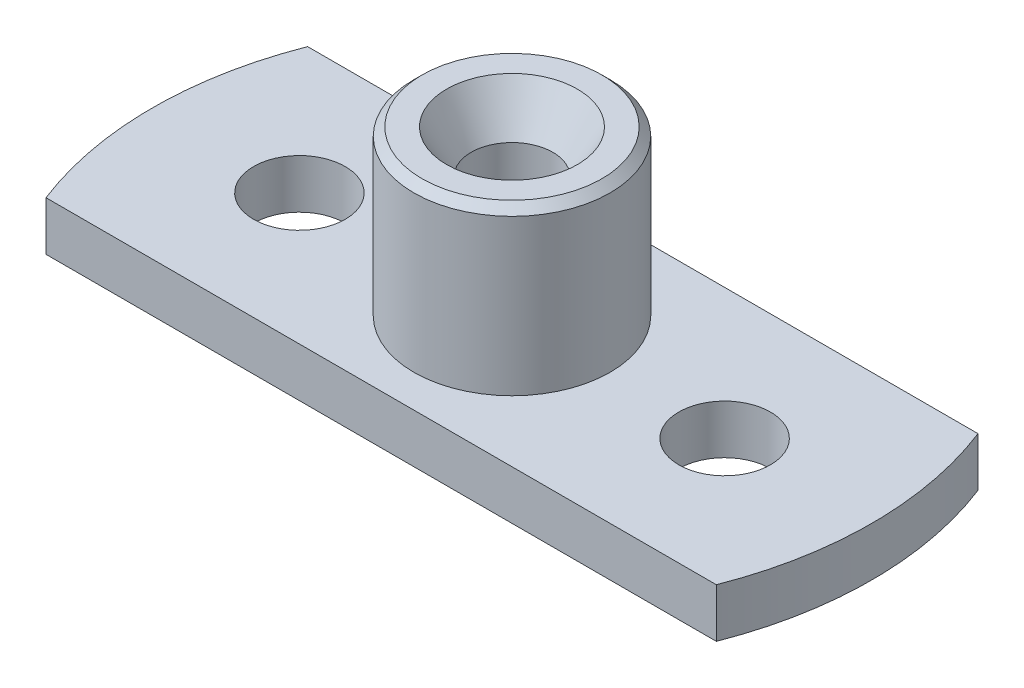
SolidWorks part; units mm, degrees
ref_plane "Front Plane" through (0, 0, 0) normal (0, 0, 1) x (1, 0, 0)
ref_plane "Top Plane" through (0, 0, 0) normal (0, 1, 0) x (1, 0, 0)
ref_plane "Right Plane" through (0, 0, 0) normal (1, 0, 0) x (0, 0, -1)
sketch "Base Sketch" plane through (0, 0, 0) normal (0, 1, 0) x (1, 0, 0)
  line L1 (-10.247, -4) -> (10.247, -4)
  line L2 (-10.247, -4) -> (-10.247, 4)
  line L3 (-10.247, 4) -> (10.247, 4)
  line L4 (10.247, -4) -> (10.247, 4)
  line L5 (-10.247, -4) -> (10.247, 4) construction
  line L6 (-10.247, 4) -> (10.247, -4) construction
  arc A0 (-10.247, 4) -> (-10.247, -4) centre (0, 0) ccw
  arc A1 (10.247, -4) -> (10.247, 4) centre (0, 0) ccw
  point P0 (0, 0)
  point P8 (-11, 0)
  point P9 (11, 0)
  dimension "D1" = 11
  dimension "D2" = 8
  dimension "D3" = 22
extrude "Base Extrude" add sketch "Base Sketch" along normal blind 1.5 contours L2 A0 | L1 L4 L3 L2 | L4 A1
sketch "Protrusion Sketch" plane through (0, 0, 0) normal (0, 1, 0) x (1, 0, 0)
  circle A0 centre (0, 0) radius 3
  dimension "D1" = 6
extrude "Protrusion Extrude" add sketch "Protrusion Sketch" along normal blind 5 from surface at 1.5 starting at face at (0, 1.5, 0)
sketch "Hole Locations Top Plane" plane through (0, 0, 0) normal (0, 1, 0) x (1, 0, 0)
  point P0 (0, 0)
  point P1 (-6.5, 0)
  point P3 (6.5, 0)
  dimension "D1" = 6.5
  dimension "D2" = 13
hole_wizard "Ø2.8 (2.8) Diameter Hole1" positions "Sketch2" profile "Sketch4" hole size "Ø2.8" standard "ANSI Metric" end condition through all
sketch "Sketch2" plane through (0, 1.5, 0) normal (0, 1, 0) x (1, 0, 0)
  point P0 (-6.5, 0)
  point P3 (6.5, 0)
sketch "Sketch4" plane through (-6.5, 1.5, 0) normal (1, 0, 0) x (0, 0, 1)
  line L0 (0, 0) -> (0, 1.5)
  line L1 (0, 1.5) -> (1.4, 1.5)
  line L2 (1.4, 1.5) -> (1.4, 0)
  line L5 (1.4, 0) -> (0, 0)
  line L11 (0, -6.35) -> (0, 107.95) construction
  dimension "Thru Hole Dia." = 2.8
  dimension "Thru Hole Depth" = 1.5
chamfer "Protrusion Chamfer" distance 0.25 1 edges at (0, 6.5, 3)
hole_wizard "Ø2.5mm Dowel Hole3" positions "Sketch18" profile "Sketch19" hole size "Ø2.5" standard "ANSI Metric" end condition up to next
sketch "Sketch18" plane through (0, 6.5, 0) normal (0, 1, 0) x (1, 0, 0)
  point P0 (0, 0)
sketch "Sketch19" plane through (0, 6.5, 0) normal (1, 0, 0) x (0, 0, 1)
  line L0 (0, 0) -> (0, 6.5)
  line L1 (0, 6.5) -> (1.25, 6.5)
  line L2 (1.25, 6.5) -> (1.25, 1.299)
  line L3 (1.25, 1.299) -> (2, 0)
  line L5 (2, 0) -> (0, 0)
  line L6 (-1.25, 1.299) -> (-2, 0) construction
  line L11 (0, -6.35) -> (0, 107.95) construction
  dimension "Thru Hole Dia." = 2.5
  dimension "Thru Hole Depth" = 6.5
  dimension "Near C'Sink Dia." = 4
  dimension "Near C'Sink Angle" = 60
sketch "5mm Circle Sketch" plane through (0, 0, 0) normal (0, 1, 0) x (1, 0, 0)
  circle A0 centre (0, 0) radius 2.5
  dimension "D1" = 5
extrude "5mm Diameter Cut" cut sketch "5mm Circle Sketch" along normal blind 0.7 from surface
